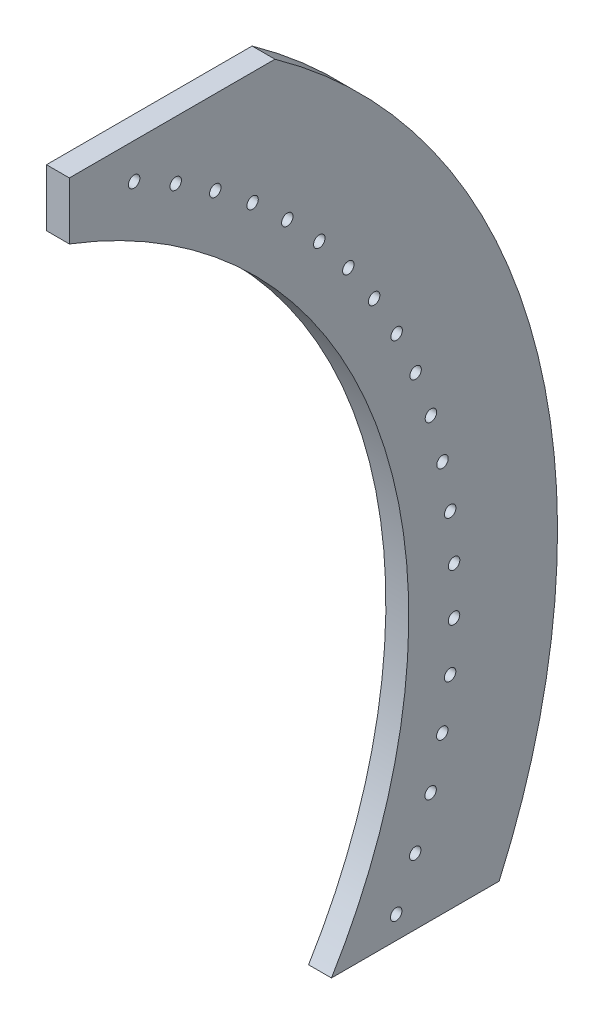
SolidWorks part; units mm, degrees
ref_plane "Front Plane" through (0, 0, 0) normal (0, 0, 1) x (1, 0, 0)
ref_plane "Top Plane" through (0, 0, 0) normal (0, 1, 0) x (1, 0, 0)
ref_plane "Right Plane" through (0, 0, 0) normal (1, 0, 0) x (0, 0, -1)
sketch "Sketch1" plane through (0, 0, 0) normal (1, 0, 0) x (0, 0, -1)
  line L0 (0, 609.6) -> (323.85, 609.6)
  line L1 (323.85, 609.6) -> (323.85, 0)
  line L2 (323.85, 0) -> (0, 0)
  line L3 (0, 609.6) -> (0, 577.85)
  line L4 (0, 0) -> (0, 31.75)
  arc A1 (0, 577.85) -> (0, 31.75) centre (-103.7599, 304.8) cw
  dimension "D4" = 292.1
  dimension "D1" = 609.6
  dimension "D2" = 323.85
  dimension "D3" = 546.1
extrude "Boss-Extrude1" add sketch "Sketch1" along normal blind 12.7
sketch "Sketch2" plane through (12.7, 0, 0) normal (1, 0, 0) x (0, 0, -1)
  line L0 (0, 0) -> (323.85, 0) construction
  line L1 (-233.5002, 152.4) -> (618.8069, 152.4)
  line L2 (-233.5002, 152.4) -> (-233.5002, 0)
  line L3 (-233.5002, 0) -> (618.8069, 0)
  line L4 (618.8069, 152.4) -> (618.8069, 0)
  dimension "D1" = 152.4
  dimension "D2" = 0
extrude "Cut-Extrude1" cut sketch "Sketch2" against normal blind 12.7
sketch "Sketch3" plane through (12.7, 0, 0) normal (1, 0, 0) x (0, 0, -1)
  line L0 (323.85, 609.6) -> (0, 609.6) construction
  line L1 (323.85, 152.4) -> (145.4321, 152.4) construction
  line L2 (270.7608, 152.4) -> (323.85, 152.4)
  line L3 (323.85, 152.4) -> (323.85, 609.6)
  line L4 (323.85, 609.6) -> (161.925, 609.6)
  arc A0 (161.925, 609.6) -> (270.7608, 152.4) centre (-103.7599, 304.8) cw
extrude "Cut-Extrude2" cut sketch "Sketch3" against normal blind 12.7
hole_wizard "1/4 (0.25) Diameter Hole1" positions "Sketch4" profile "Sketch5" hole size "1/4" standard "ANSI Inch" end condition through all
sketch "Sketch4" plane through (12.7, 0, 0) normal (1, 0, 0) x (0, 0, -1)
  line L0 (270.7608, 152.4) -> (145.4321, 152.4) construction
  arc A0 (145.4321, 152.4) -> (0, 577.85) centre (-103.7599, 304.8) ccw construction
  circle A1 centre (-103.7599, 304.8) radius 317.5 construction
  point P0 (181.3544, 165.1)
  point P26 (191.917, 189.1217)
  point P27 (200.4597, 213.9336)
  point P28 (206.9243, 239.3662)
  point P29 (211.2667, 265.2458)
  point P30 (213.4571, 291.3956)
  point P31 (213.4805, 317.6369)
  point P32 (211.3369, 343.7906)
  point P33 (207.0409, 369.6779)
  point P34 (200.6218, 395.122)
  point P35 (192.1234, 419.9492)
  point P36 (181.6039, 443.9897)
  point P37 (169.135, 467.0795)
  point P38 (154.802, 489.0607)
  point P39 (138.7028, 509.7832)
  point P40 (120.9473, 529.1055)
  point P41 (101.6568, 546.8955)
  point P42 (80.9631, 563.0318)
  point P43 (59.0076, 577.4041)
  point P44 (35.9401, 589.9143)
  dimension "D1" = 12.7
  dimension "D2" = 317.5
  dimension "D3" = 20
sketch "Sketch5" plane through (12.7, 165.1, -181.3544) normal (0, 1, 0) x (0, 0, -1)
  line L0 (0, 0) -> (0, 12.7)
  line L1 (0, 12.7) -> (3.175, 12.7)
  line L2 (3.175, 12.7) -> (3.175, 0)
  line L5 (3.175, 0) -> (0, 0)
  line L11 (0, -6.35) -> (0, 107.95) construction
  dimension "Thru Hole Dia." = 6.35
  dimension "Thru Hole Depth" = 12.7
sketch "Sketch6" plane through (12.7, 0, 0) normal (1, 0, 0) x (0, 0, -1)
  line L0 (161.925, 609.6) -> (114.0923, 609.6)
  line L1 (161.925, 609.6) -> (0, 609.6) construction
  line L2 (270.7608, 152.4) -> (238.4928, 152.4)
  line L3 (270.7608, 152.4) -> (145.4321, 152.4) construction
  arc A0 (238.4928, 152.4) -> (114.0923, 609.6) centre (-103.7599, 304.8) ccw
  arc A1 (270.7608, 152.4) -> (161.925, 609.6) centre (-103.7599, 304.8) ccw
extrude "Cut-Extrude3" cut sketch "Sketch6" against normal through all contours A1 L0 A0 L2
